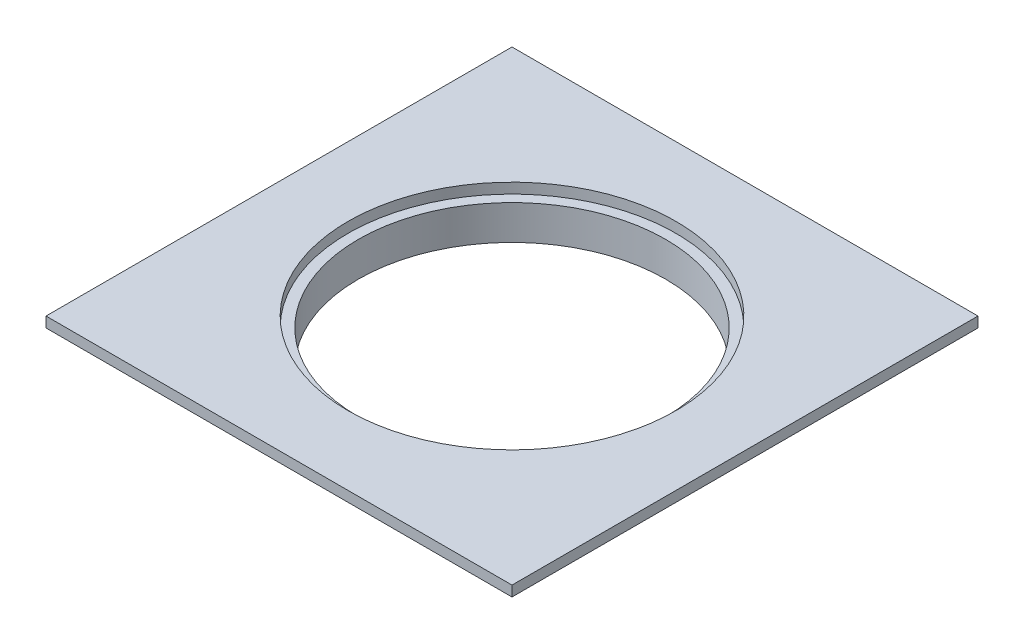
SolidWorks part; units mm, degrees
material "1060 Alloy"
ref_plane "Front" through (0, 0, 0) normal (0, 0, 1) x (1, 0, 0)
ref_plane "Top" through (0, 0, 0) normal (0, 1, 0) x (1, 0, 0)
ref_plane "Right" through (0, 0, 0) normal (1, 0, 0) x (0, 0, -1)
sketch "Sketch1" plane through (0, 0, 0) normal (0, 1, 0) x (1, 0, 0)
  line L1 (-67.5, -67.5) -> (67.5, -67.5)
  line L2 (-67.5, -67.5) -> (-67.5, 67.5)
  line L3 (-67.5, 67.5) -> (67.5, 67.5)
  line L4 (67.5, -67.5) -> (67.5, 67.5)
  line L5 (-67.5, -67.5) -> (67.5, 67.5) construction
  line L6 (-67.5, 67.5) -> (67.5, -67.5) construction
  circle A0 centre (0, 0) radius 47.5
  point P0 (0, 0)
  dimension "D3" = 95
  dimension "D1" = 135
  dimension "D2" = 135
extrude "Boss-Extrude1" add sketch "Sketch1" along normal blind 3
sketch "Sketch2" plane through (0, 0, 0) normal (0, -1, 0) x (1, 0, 0)
  circle A0 centre (0, 0) radius 55
  circle A1 centre (0, 0) radius 44.5
  dimension "D1" = 89
  dimension "D2" = 110
extrude "Boss-Extrude2" add sketch "Sketch2" along normal blind 10 contours A1 | A0
